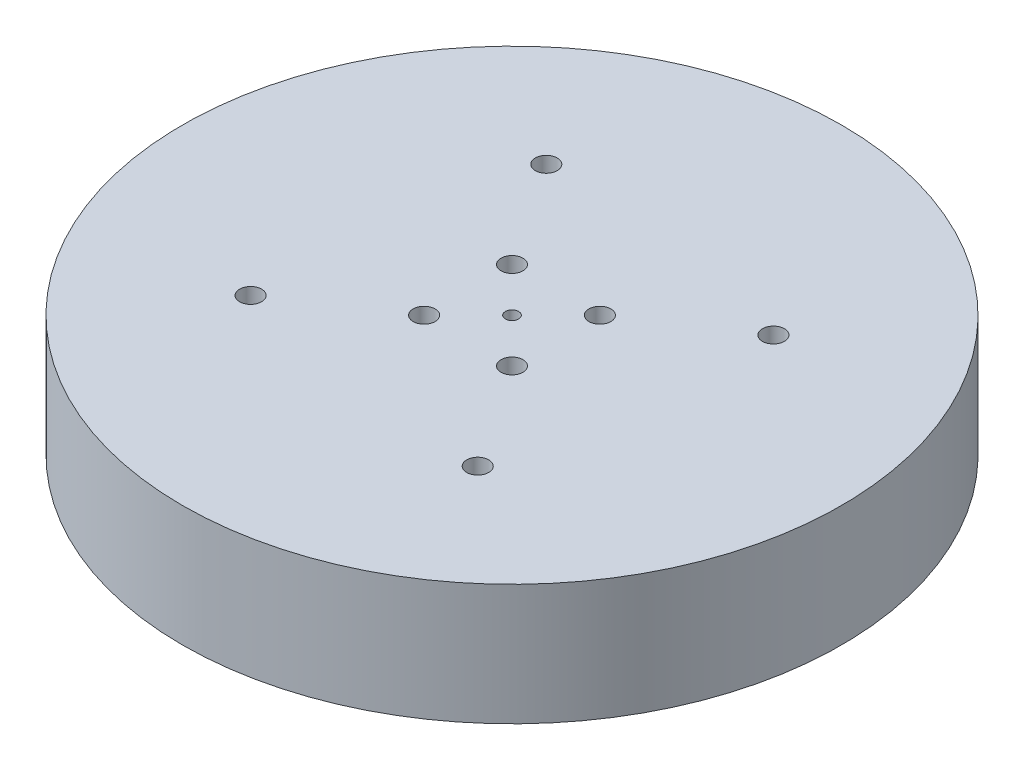
SolidWorks part; units mm, degrees
ref_plane "Front Plane" through (0, 0, 0) normal (0, 0, 1) x (1, 0, 0)
ref_plane "Top Plane" through (0, 0, 0) normal (0, 1, 0) x (1, 0, 0)
ref_plane "Right Plane" through (0, 0, 0) normal (1, 0, 0) x (0, 0, -1)
sketch "Sketch1" plane through (0, 0, 0) normal (0, 1, 0) x (1, 0, 0)
  circle A0 centre (0, 0) radius 75
  circle A1 centre (0, 0) radius 70
  dimension "D1" = 150
  dimension "D2" = 140
extrude "Boss-Extrude1" add sketch "Sketch1" along normal blind 22.5
sketch "Sketch2" plane through (0, 22.5, 0) normal (0, 1, 0) x (1, 0, 0)
  circle A0 centre (0, 0) radius 75
extrude "Boss-Extrude2" add sketch "Sketch2" along normal blind 5
sketch "Sketch4" plane through (0, 27.5, 0) normal (0, 1, 0) x (1, 0, 0)
  circle A0 centre (0, 0) radius 1.5
  dimension "D1" = 3
extrude "Cut-Extrude2" cut sketch "Sketch4" against normal up to surface (5 mm away) up to face at (0, 22.5, 70)
sketch "Sketch5" plane through (0, 27.5, 0) normal (0, 1, 0) x (1, 0, 0)
  circle A0 centre (-10, 10) radius 2.5
  dimension "D3" = 5
  dimension "D1" = 10
  dimension "D2" = 10
extrude "Cut-Extrude3" cut sketch "Sketch5" against normal blind 10
pattern_linear "LPattern1" count 2 spacing 20 along (0, 0, 1) count 2 spacing 20 along (1, 0, 0) of "Cut-Extrude3"
sketch "Sketch6" plane through (0, 27.5, 0) normal (0, 1, 0) x (1, 0, 0)
  circle A0 centre (-25.8448, 33.6459) radius 2.5
  circle A1 centre (33.6459, 25.8448) radius 2.5
  circle A2 centre (-33.6459, -25.8448) radius 2.5
  circle A3 centre (25.8448, -33.6459) radius 2.5
extrude "Cut-Extrude4" cut sketch "Sketch6" against normal blind 10
sketch "Sketch7" plane through (0, 22.5, 0) normal (0, -1, 0) x (1, 0, 0)
  line L1 (-31.3365, 29.8448) -> (-35.9553, 29.8448)
  line L2 (-35.9553, 29.8448) -> (-38.2647, 25.8448)
  line L3 (-38.2647, 25.8448) -> (-35.9553, 21.8448)
  line L4 (-35.9553, 21.8448) -> (-31.3365, 21.8448)
  line L5 (-31.3365, 21.8448) -> (-29.0271, 25.8448)
  line L6 (-29.0271, 25.8448) -> (-31.3365, 29.8448)
  line L7 (28.1542, 37.6459) -> (23.5354, 37.6459)
  line L8 (23.5354, 37.6459) -> (21.226, 33.6459)
  line L9 (21.226, 33.6459) -> (23.5354, 29.6459)
  line L10 (23.5354, 29.6459) -> (28.1542, 29.6459)
  line L11 (28.1542, 29.6459) -> (30.4636, 33.6459)
  line L12 (30.4636, 33.6459) -> (28.1542, 37.6459)
  line L13 (35.9553, -21.8448) -> (31.3365, -21.8448)
  line L14 (31.3365, -21.8448) -> (29.0271, -25.8448)
  line L15 (29.0271, -25.8448) -> (31.3365, -29.8448)
  line L16 (31.3365, -29.8448) -> (35.9553, -29.8448)
  line L17 (35.9553, -29.8448) -> (38.2647, -25.8448)
  line L18 (38.2647, -25.8448) -> (35.9553, -21.8448)
  line L19 (-23.5354, -29.6459) -> (-28.1542, -29.6459)
  line L20 (-28.1542, -29.6459) -> (-30.4636, -33.6459)
  line L21 (-30.4636, -33.6459) -> (-28.1542, -37.6459)
  line L22 (-28.1542, -37.6459) -> (-23.5354, -37.6459)
  line L23 (-23.5354, -37.6459) -> (-21.226, -33.6459)
  line L24 (-21.226, -33.6459) -> (-23.5354, -29.6459)
  circle A0 centre (-33.6459, 25.8448) radius 4 construction
  circle A1 centre (25.8448, 33.6459) radius 4 construction
  circle A2 centre (33.6459, -25.8448) radius 4 construction
  circle A3 centre (-25.8448, -33.6459) radius 4 construction
  dimension "D1" = 8
  dimension "D2" = 8
  dimension "D3" = 8
  dimension "D4" = 8
sketch "Sketch8" plane through (0, 22.5, 0) normal (0, -1, 0) x (1, 0, 0)
  circle A0 centre (-33.6459, 25.8448) radius 7.5
  circle A1 centre (25.8448, 33.6459) radius 7.5
  circle A2 centre (33.6459, -25.8448) radius 7.5
  circle A3 centre (-25.8448, -33.6459) radius 7.5
  dimension "D1" = 15
extrude "Boss-Extrude3" add sketch "Sketch8" along normal blind 7
extrude "Cut-Extrude5" cut sketch "Sketch7" along normal blind 7
